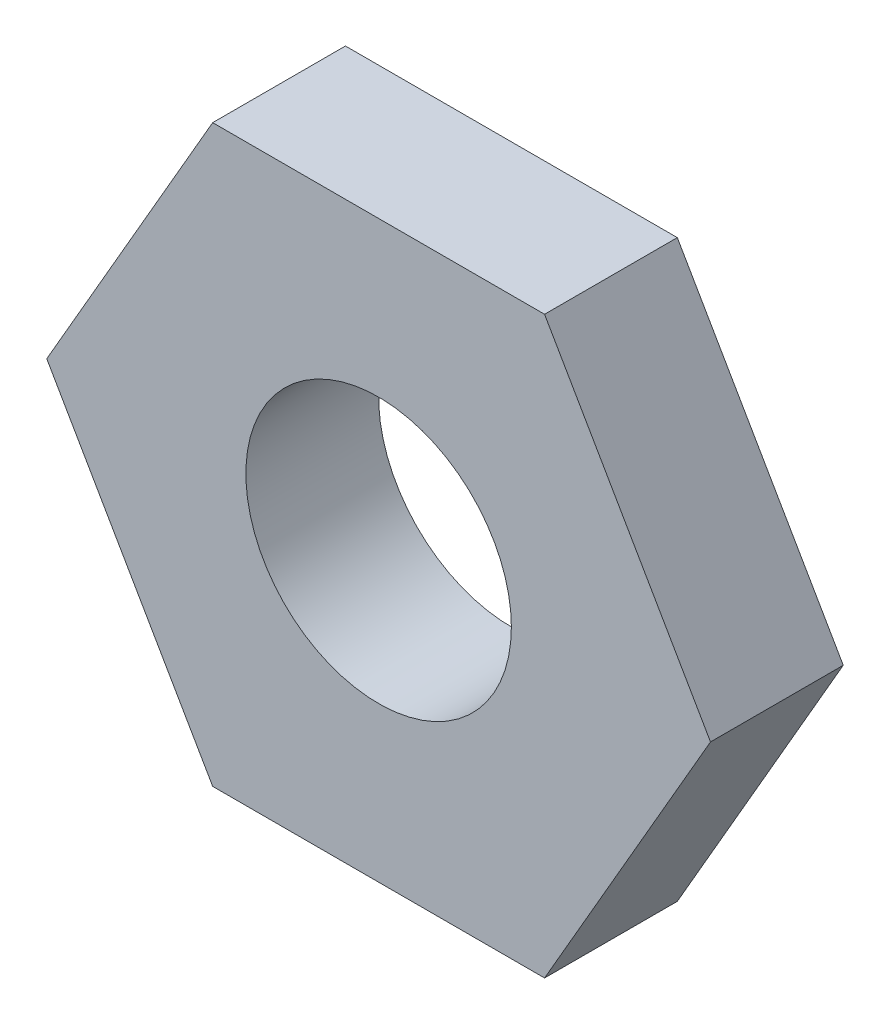
SolidWorks part; units mm, degrees
ref_plane "Front" through (0, 0, 0) normal (0, 0, 1) x (1, 0, 0)
ref_plane "Top" through (0, 0, 0) normal (0, 1, 0) x (1, 0, 0)
ref_plane "Right" through (0, 0, 0) normal (1, 0, 0) x (0, 0, -1)
sketch "Sketch1" plane through (0, 0, 0) normal (0, 0, 1) x (1, 0, 0)
  line L1 (-10, 0) -> (-5, -8.6603)
  line L2 (-5, -8.6603) -> (5, -8.6603)
  line L3 (5, -8.6603) -> (10, 0)
  line L4 (10, 0) -> (5, 8.6603)
  line L5 (5, 8.6603) -> (-5, 8.6603)
  line L6 (-5, 8.6603) -> (-10, 0)
  circle A0 centre (0, 0) radius 8.6603 construction
  dimension "D1" = 10
extrude "Boss-Extrude1" add sketch "Sketch1" along normal blind 4
sketch "Sketch2" plane through (0, 0, 4) normal (0, 0, 1) x (1, 0, 0)
  circle A0 centre (0, 0) radius 4
  dimension "D1" = 8
extrude "Cut-Extrude1" cut sketch "Sketch2" against normal through all
